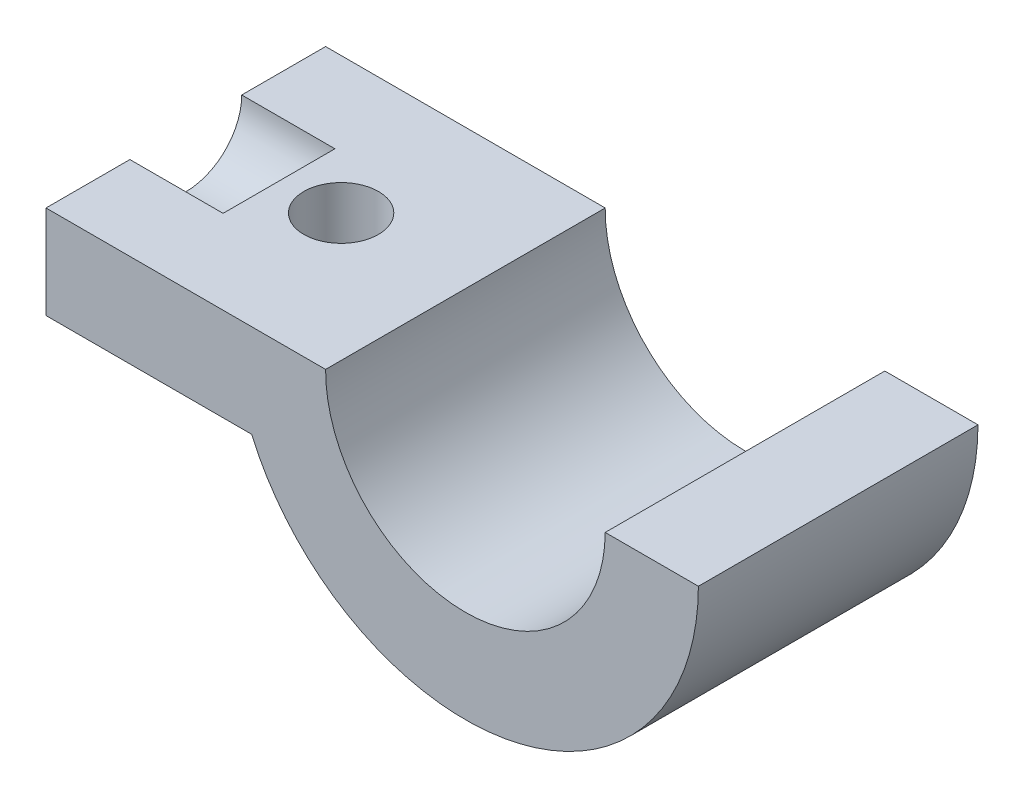
SolidWorks part; units mm, degrees
ref_plane "前视基准面" through (0, 0, 0) normal (0, 0, 1) x (1, 0, 0)
ref_plane "上视基准面" through (0, 0, 0) normal (0, 1, 0) x (1, 0, 0)
ref_plane "右视基准面" through (0, 0, 0) normal (1, 0, 0) x (0, 0, -1)
sketch "草图2" plane through (0, 0, 0) normal (0, 0, 1) x (1, 0, 0)
  line L0 (9.25, -2.3869) -> (7.75, -2.3869)
  line L1 (7.75, -2.3869) -> (7.75, -2.8869)
  line L2 (7.75, -2.8869) -> (8.8531, -2.8869)
  line L3 (10.75, -2.3944) -> (11.25, -2.3944)
  arc A0 (9.25, -2.3869) -> (10.75, -2.3944) centre (10, -2.3907) ccw
  arc A1 (8.8531, -2.8869) -> (11.25, -2.3944) centre (10, -2.3897) ccw
  dimension "D1" = 0.5
  dimension "D2" = 2.5
extrude "凸台-拉伸1" add sketch "草图2" against normal blind 1.5
sketch "草图3" plane through (7.75, 0, 0) normal (-1, 0, 0) x (0, 0, 1)
  line L0 (-1.5, -2.3869) -> (0, -2.3869) construction
  circle A0 centre (-0.75, -2.3869) radius 0.3
extrude "切除-拉伸1" cut sketch "草图3" against normal blind 0.5
sketch "草图4" plane through (0, -2.3869, 0) normal (0, 1, 0) x (1, 0, 0)
  circle A0 centre (8.5648, 0.7685) radius 0.2
extrude "切除-拉伸2" cut sketch "草图4" against normal blind 0.5
